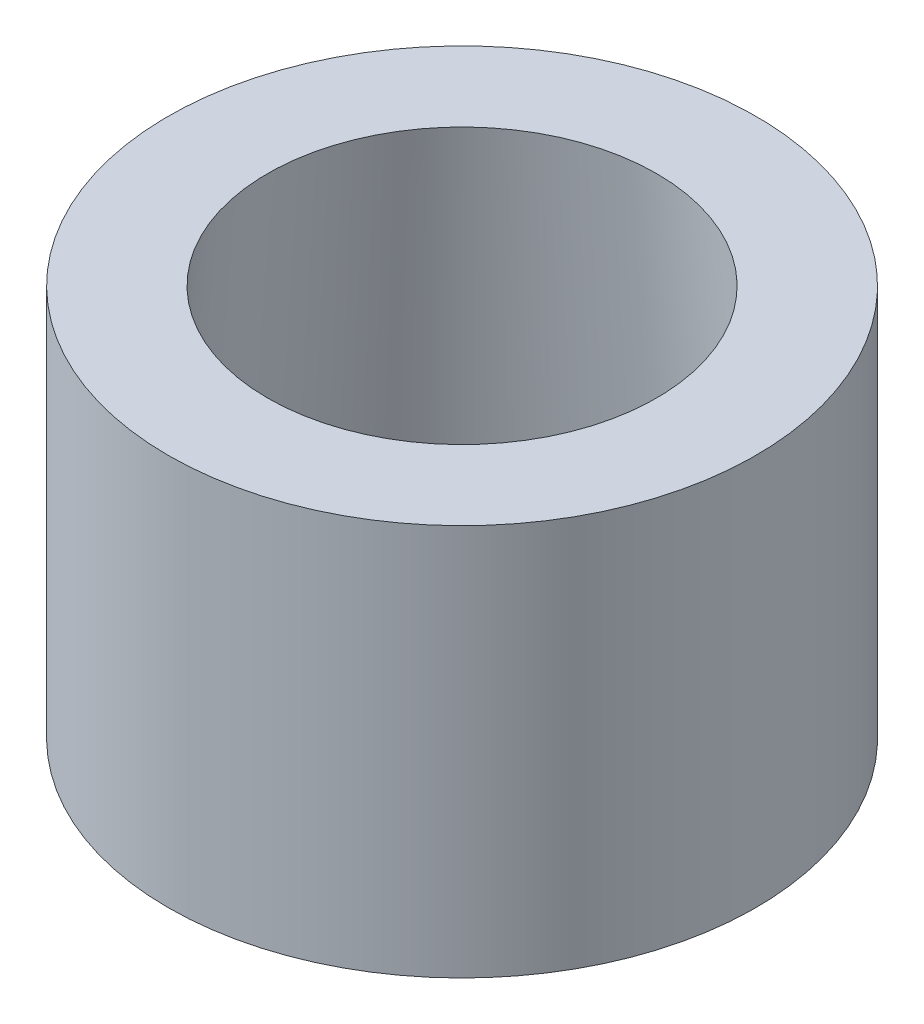
SolidWorks part; units mm, degrees
ref_plane "Front Plane" through (0, 0, 0) normal (0, 0, 1) x (1, 0, 0)
ref_plane "Top Plane" through (0, 0, 0) normal (0, 1, 0) x (1, 0, 0)
ref_plane "Right Plane" through (0, 0, 0) normal (1, 0, 0) x (0, 0, -1)
sketch "Sketch1" plane through (0, 0, 0) normal (0, 1, 0) x (1, 0, 0)
  circle A1 centre (0, 0) radius 19.05
  dimension "D1" = 38.1
extrude "Boss-Extrude1" add sketch "Sketch1" along normal blind 25.4
sketch "Sketch2" plane through (0, 0, 0) normal (0, -1, 0) x (1, 0, 0)
  circle A1 centre (0, 0) radius 14.732
  dimension "D1" = 29.464
sketch "Sketch3" plane through (0, 25.4, 0) normal (0, 1, 0) x (1, 0, 0)
  circle A0 centre (0, 0) radius 12.6111
  dimension "D1" = 25.2222
loft "Cut-Loft2" cut profiles "Sketch3", "Sketch2"
